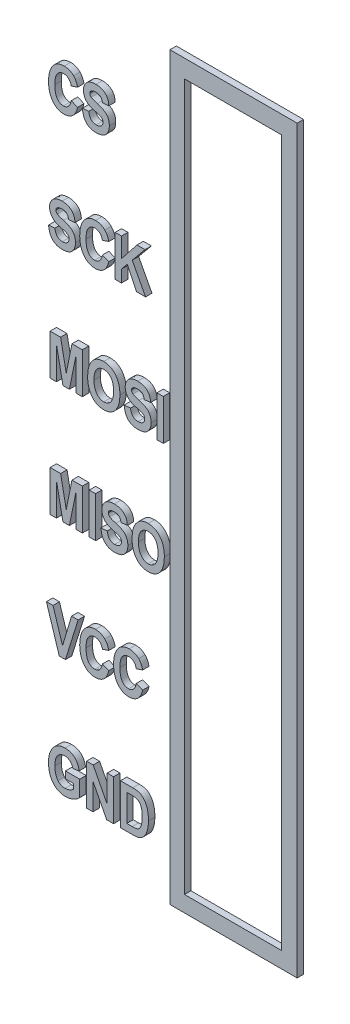
SolidWorks part; units mm, degrees
ref_plane "Plan de face" through (0, 0, 0) normal (0, 0, 1) x (1, 0, 0)
ref_plane "Plan de dessus" through (0, 0, 0) normal (0, 1, 0) x (1, 0, 0)
ref_plane "Plan de droite" through (0, 0, 0) normal (1, 0, 0) x (0, 0, -1)
sketch "Esquisse2" plane through (0, 0, 0) normal (0, 0, 1) x (1, 0, 0)
  line L1 (-40.5592, -15.9698) -> (-35.0592, -15.9698)
  line L2 (-40.5592, -15.9698) -> (-40.5592, -31.9698)
  line L3 (-40.5592, -31.9698) -> (-35.0592, -31.9698)
  line L4 (-35.0592, -15.9698) -> (-35.0592, -31.9698)
  circle A0 centre (-39.0592, -30.3198) radius 0.5
  circle A1 centre (-39.0592, -27.7798) radius 0.5
  circle A2 centre (-39.0592, -25.2398) radius 0.5
  circle A3 centre (-39.0592, -22.6998) radius 0.5
  circle A4 centre (-39.0592, -20.1598) radius 0.5
  circle A5 centre (-39.0592, -17.6198) radius 0.5
  circle A7 centre (-39.0592, -15.0798) radius 0.5 [skipped]
  dimension "D3" = 1.5
  dimension "D4" = 7
  dimension "D5" = 1.65
  dimension "D6" = 1.65
  dimension "D1" = 16
  dimension "D2" = 5.5
extrude "Boss.-Extru.1" add sketch "Esquisse2" along normal blind 0.3
sketch "Esquisse3" plane through (0, 0, 0.3) normal (0, 0, 1) x (1, 0, 0)
  line L0 (-40.5592, -31.9698) -> (-35.0592, -31.9698) construction
  line L1 (-40.5592, -15.9698) -> (-37.8092, -15.9698)
  line L2 (-40.5592, -15.9698) -> (-40.5592, -31.9698)
  line L3 (-40.5592, -31.9698) -> (-37.8092, -31.9698)
  line L4 (-37.8092, -15.9698) -> (-37.8092, -31.9698)
  line L6 (-40.2449, -16.3582) -> (-38.1517, -16.3582)
  line L7 (-40.2449, -16.3582) -> (-40.2449, -31.6241)
  line L8 (-40.2449, -31.6241) -> (-38.1517, -31.6241)
  line L9 (-38.1517, -16.3582) -> (-38.1517, -31.6241)
extrude "Boss.-Extru.2" add sketch "Esquisse3" along normal blind 0.15
sketch "Esquisse7" plane through (0, 0, 0.3) normal (0, 0, 1) x (1, 0, 0)
  line L1 (-40.5592, -15.9698) -> (-44.3308, -15.9698)
  line L2 (-40.5592, -15.9698) -> (-40.5592, -31.9698)
  line L3 (-40.5592, -31.9698) -> (-44.3308, -31.9698)
  line L4 (-44.3308, -15.9698) -> (-44.3308, -31.9698)
extrude "Boss.-Extru.6" add sketch "Esquisse7" against normal blind 0.3
sketch "Esquisse8" plane through (0, 0, 0) normal (0, 1, 0) x (1, 0, 0)
  line L1 (-37.8092, -0.3) -> (-34.6192, -0.3)
  line L2 (-37.8092, -0.3) -> (-37.8092, 0.8405)
  line L3 (-37.8092, 0.8405) -> (-34.6192, 0.8405)
  line L4 (-34.6192, -0.3) -> (-34.6192, 0.8405)
extrude "Enlèv. mat.-Extru.2" cut sketch "Esquisse8" against normal blind 44.3
sketch "Esquisse9" plane through (0, 0, 0.3) normal (0, 0, 1) x (1, 0, 0)
  text T0 "CS\r\nSCK\r\nMOSI\r\nMISO\r\nVCC\r\nGND" font "Arial Narrow" height 0.88
extrude "Boss.-Extru.7" add sketch "Esquisse9" along normal blind 0.15
sketch "Esquisse10" plane through (0, 0, 0.3) normal (0, 0, 1) x (1, 0, 0)
  line L1 (-39.8039, -16.7638) -> (-38.4219, -16.7638)
  line L2 (-39.8039, -16.7638) -> (-39.8039, -31.4062)
  line L3 (-39.8039, -31.4062) -> (-38.4219, -31.4062)
  line L4 (-38.4219, -16.7638) -> (-38.4219, -31.4062)
extrude "Boss.-Extru.8" add sketch "Esquisse10" against normal blind 0.3
sketch "Esquisse11" plane through (0, -15.9698, 0) normal (0, 1, 0) x (1, 0, 0)
  line L1 (-44.4688, 0.3379) -> (-37.7404, 0.3379)
  line L2 (-44.4688, 0.3379) -> (-44.4688, -0.3112)
  line L3 (-44.4688, -0.3112) -> (-37.7404, -0.3112)
  line L4 (-37.7404, 0.3379) -> (-37.7404, -0.3112)
extrude "Enlèv. mat.-Extru.3" cut sketch "Esquisse11" against normal blind 23 and the other way blind 13
